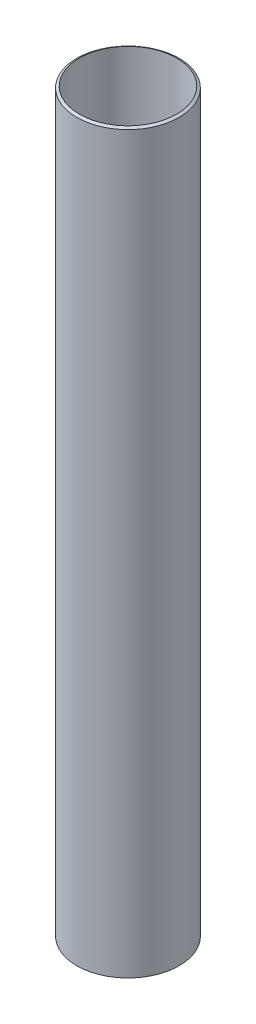
SolidWorks part; units mm, degrees
material "6061-T6 (SS)"
ref_plane "Front Plane" through (0, 0, 0) normal (0, 0, 1) x (1, 0, 0)
ref_plane "Top Plane" through (0, 0, 0) normal (0, 1, 0) x (1, 0, 0)
ref_plane "Right Plane" through (0, 0, 0) normal (1, 0, 0) x (0, 0, -1)
ref_axis "Axis1" through (0, 819.187, 0) along (0, -1, 0)
sketch "Sketch2" plane through (0, 0, 0) normal (0, 0, 1) x (1, 0, 0)
  line L0 (-63.5, 1.8331) -> (-63.5, 912.5669)
  line L1 (-60.325, 0) -> (-63.5, 1.8331)
  line L2 (-60.325, 0) -> (-60.325, 914.4)
  line L3 (55, 0) -> (-55, 0) construction
  line L4 (-63.5, 457.2) -> (-59.436, 457.2) construction
  line L5 (0, 819.187) -> (0, -55) construction
  line L6 (-60.325, 914.4) -> (-63.5, 912.5669)
  point P0 (-60.4938, -3.2627)
  point P1 (-63.5, 457.2)
  point P17 (-60.325, 457.2)
  dimension "D1" = 457.2
  dimension "D2" = 3.175
  dimension "D4" = 63.5
  dimension "D5" = 120
revolve "Revolve1" add sketch "Sketch2" angle 360 about axis through (0, 819.187, 0) along (0, -1, 0)
